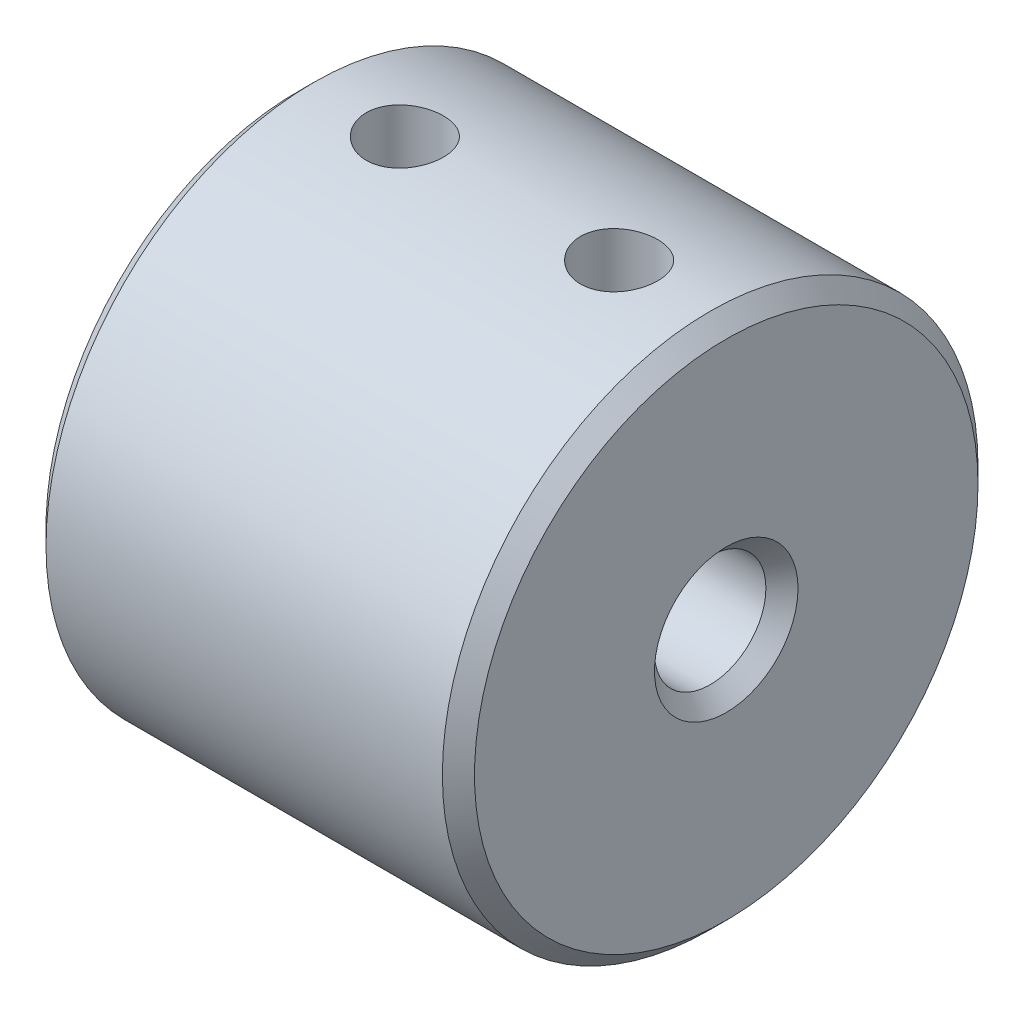
SolidWorks part; units mm, degrees
ref_plane "Front Plane" through (0, 0, 0) normal (0, 0, 1) x (1, 0, 0)
ref_plane "Top Plane" through (0, 0, 0) normal (0, 1, 0) x (1, 0, 0)
ref_plane "Right Plane" through (0, 0, 0) normal (1, 0, 0) x (0, 0, -1)
sketch "Sketch1" plane through (0, 0, 0) normal (1, 0, 0) x (0, 0, -1)
  circle A0 centre (0, 0) radius 5.1
  circle A1 centre (0, 0) radius 12.5
  dimension "D1" = 10.2
  dimension "D2" = 25
extrude "Boss-Extrude1" add sketch "Sketch1" along normal blind 20 contours A1
sketch "Sketch2" plane through (20, 0, 0) normal (1, 0, 0) x (0, 0, -1)
  circle A1 centre (0, 0) radius 5.1 construction
  circle A2 centre (0, 0) radius 5.1
  circle A3 centre (0, 0) radius 2.6
  dimension "D1" = 5.2
extrude "Boss-Extrude2" add sketch "Sketch2" against normal blind 10 contours A3
sketch "Sketch3" plane through (0, 0, 0) normal (0, 1, 0) x (1, 0, 0)
  line L2 (20, 0) -> (0, 0) construction
  line L3 (20, -2.6) -> (20, 2.6) construction
  circle A0 centre (5, 0) radius 1.8
  circle A1 centre (15, 0) radius 1.8
  dimension "D1" = 3.6
  dimension "D2" = 5
  dimension "D3" = 5
extrude "Cut-Extrude1" cut sketch "Sketch3" along normal up to next contours A0 | A1
chamfer "Chamfer1" distance 0.75 angle 45 5 edges at (20, 0, -2.6) (20, 0, -12.5) (0, 0, -5.1) (10, 0, -5.1) (0, 0, -12.5)
